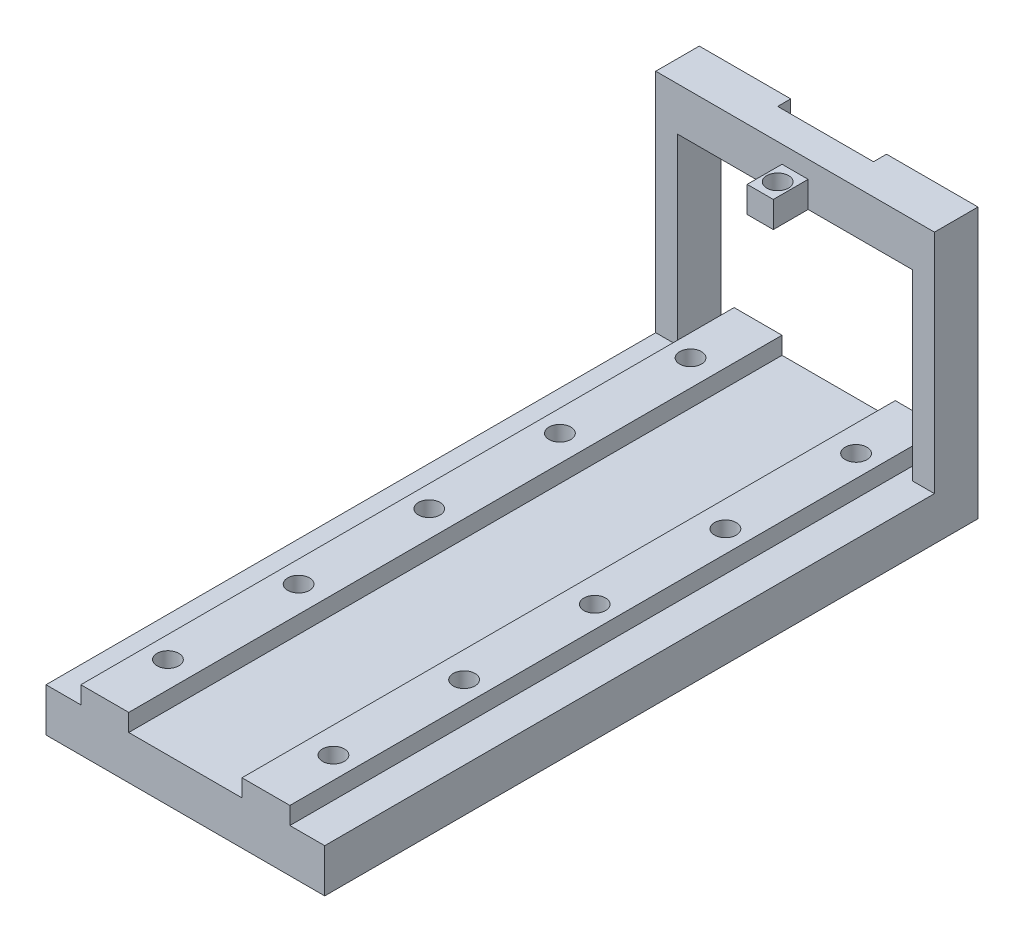
SolidWorks part; units mm, degrees
ref_plane "Front Plane" through (0, 0, 0) normal (0, 0, 1) x (1, 0, 0)
ref_plane "Top Plane" through (0, 0, 0) normal (0, 1, 0) x (1, 0, 0)
ref_plane "Right Plane" through (0, 0, 0) normal (1, 0, 0) x (0, 0, -1)
sketch "Sketch1" plane through (0, 0, 0) normal (0, 1, 0) x (1, 0, 0)
  line L1 (-13.4239, -67.3549) -> (18.5761, -67.3549)
  line L2 (-13.4239, -67.3549) -> (-13.4239, 7.6451)
  line L3 (-13.4239, 7.6451) -> (18.5761, 7.6451)
  line L4 (18.5761, -67.3549) -> (18.5761, 7.6451)
  dimension "D1" = 32
  dimension "D2" = 75
extrude "Boss-Extrude1" add sketch "Sketch1" along normal blind 5
sketch "Sketch5" plane through (0, 5, 0) normal (0, 1, 0) x (1, 0, 0)
  line L1 (-13.4239, 7.6451) -> (-10.9239, 7.6451)
  line L2 (-13.4239, 7.6451) -> (-13.4239, 2.6451)
  line L3 (-13.4239, 2.6451) -> (-10.9239, 2.6451)
  line L4 (-10.9239, 7.6451) -> (-10.9239, 2.6451)
  line L5 (18.5761, 7.6451) -> (16.0761, 7.6451)
  line L6 (18.5761, 7.6451) -> (18.5761, 2.6451)
  line L7 (18.5761, 2.6451) -> (16.0761, 2.6451)
  line L8 (16.0761, 7.6451) -> (16.0761, 2.6451)
  dimension "D1" = 2.5
  dimension "D2" = 5
  dimension "D3" = 5
  dimension "D4" = 2.5
extrude "Boss-Extrude2" add sketch "Sketch5" along normal blind 26
sketch "Sketch7" plane through (16.0761, 0, 0) normal (-1, 0, 0) x (0, 0, 1)
  line L0 (-2.6451, 31) -> (-2.6451, 5) construction
  line L1 (-7.6451, 31) -> (-2.6451, 31)
  line L2 (-7.6451, 31) -> (-7.6451, 26)
  line L3 (-7.6451, 26) -> (-2.6451, 26)
  line L4 (-2.6451, 31) -> (-2.6451, 26)
  dimension "D1" = 5
extrude "Boss-Extrude3" add sketch "Sketch7" along normal blind 27
sketch "Sketch8" plane through (0, 0, -7.6451) normal (0, 0, -1) x (-1, 0, 0)
  line L0 (10.9239, 26) -> (-16.0761, 26) construction
  line L1 (2.9239, 26) -> (-8.0761, 26)
  line L2 (2.9239, 26) -> (2.9239, 31)
  line L3 (2.9239, 31) -> (-8.0761, 31)
  line L4 (-8.0761, 26) -> (-8.0761, 31)
  line L5 (-18.5761, 31) -> (13.4239, 31) construction
  dimension "D1" = 10.5
  dimension "D2" = 10.5
extrude "Cut-Extrude1" cut sketch "Sketch8" against normal blind 1.5
sketch "Sketch9" plane through (0, 0, -2.6451) normal (0, 0, 1) x (1, 0, 0)
  line L0 (-10.9239, 26) -> (16.0761, 26) construction
  line L1 (4.0761, 26) -> (1.0761, 26)
  line L2 (4.0761, 26) -> (4.0761, 29)
  line L3 (4.0761, 29) -> (1.0761, 29)
  line L4 (1.0761, 26) -> (1.0761, 29)
  line L5 (18.5761, 31) -> (18.5761, 5) construction
  line L6 (-13.4239, 31) -> (-13.4239, 5) construction
  dimension "D1" = 14.5
  dimension "D2" = 14.5
  dimension "D3" = 3
extrude "Boss-Extrude4" add sketch "Sketch9" along normal blind 4
sketch "Sketch10" plane through (0, 26, 0) normal (0, -1, 0) x (-1, 0, 0)
  line L0 (-1.0761, -1.3549) -> (-4.0761, -1.3549) construction
  line L2 (-4.0761, -1.3549) -> (-4.0761, 2.6451) construction
  circle A0 centre (-2.5761, 0.6451) radius 1.25
  dimension "D3" = 2.5
  dimension "D1" = 2
  dimension "D2" = 1.5
extrude "Cut-Extrude2" cut sketch "Sketch10" against normal blind 3
sketch "Sketch11" plane through (0, 5, 0) normal (0, 1, 0) x (1, 0, 0)
  line L0 (-13.4239, -67.3549) -> (18.5761, -67.3549) construction
  line L1 (-9.4239, -67.3549) -> (-3.9239, -67.3549)
  line L2 (-9.4239, -67.3549) -> (-9.4239, 7.6451)
  line L3 (-9.4239, 7.6451) -> (-3.9239, 7.6451)
  line L4 (-3.9239, -67.3549) -> (-3.9239, 7.6451)
  line L5 (16.0761, 7.6451) -> (-10.9239, 7.6451) construction
  line L6 (9.0761, 7.6451) -> (14.5761, 7.6451)
  line L7 (9.0761, 7.6451) -> (9.0761, -67.3549)
  line L8 (9.0761, -67.3549) -> (14.5761, -67.3549)
  line L9 (14.5761, 7.6451) -> (14.5761, -67.3549)
  point P6 (-3.9239, -29.8549)
  point P7 (-9.4239, -29.8549)
  point P15 (14.5761, -29.8549)
  point P17 (9.0761, -29.8549)
  dimension "D2" = 4
  dimension "D1" = 75
  dimension "D3" = 5.5
  dimension "D4" = 4
  dimension "D5" = 5.5
extrude "Boss-Extrude5" add sketch "Sketch11" along normal blind 2
hole_wizard "Tap Drill for M3x0.5 Tap1" positions "3DSketch1" profile "Sketch12" hole size "M3x0.5" standard "ANSI Metric" end condition through all
sketch3d "3DSketch1"
  line L0 (18.5761, 0, -7.6451) -> (-13.4239, 0, -7.6451) construction
  line L1 (18.5761, 0, 67.3549) -> (18.5761, 0, -7.6451) construction
  line L2 (-13.4239, 0, -7.6451) -> (-13.4239, 0, 67.3549) construction
  point P0 (12.0761, 0, 59.8549)
  point P2 (12.0761, 0, 44.8549)
  point P4 (12.0761, 0, 29.8549)
  point P6 (12.0761, 0, 14.8549)
  point P8 (12.0761, 0, -0.1451)
  point P10 (-6.9239, 0, 59.8549)
  point P12 (-6.9239, 0, 44.8549)
  point P14 (-6.9239, 0, 29.8549)
  point P16 (-6.9239, 0, 14.8549)
  point P18 (-6.9239, 0, -0.1451)
  dimension "D1" = 7.5
  dimension "D2" = 6.5
  dimension "D3" = 15
  dimension "D4" = 6.5
  dimension "D5" = 6.5
  dimension "D6" = 15
  dimension "D7" = 15
  dimension "D8" = 6.5
  dimension "D9" = 15
  dimension "D10" = 6.5
  dimension "D11" = 6.5
  dimension "D12" = 7.5
  dimension "D13" = 6.5
  dimension "D14" = 6.5
  dimension "D15" = 6.5
  dimension "D16" = 6.5
  dimension "D17" = 15
  dimension "D18" = 15
  dimension "D19" = 15
  dimension "D20" = 15
sketch "Sketch12" plane through (12.0761, 0, 59.8549) normal (1, 0, 0) x (0, 0, -1)
  line L0 (0, 0) -> (0, 31)
  line L1 (0, 31) -> (1.25, 31)
  line L2 (1.25, 31) -> (1.25, 0)
  line L5 (1.25, 0) -> (0, 0)
  line L11 (0, -6.35) -> (0, 107.95) construction
  dimension "Thru Hole Dia." = 2.5
  dimension "Thru Hole Depth" = 31
